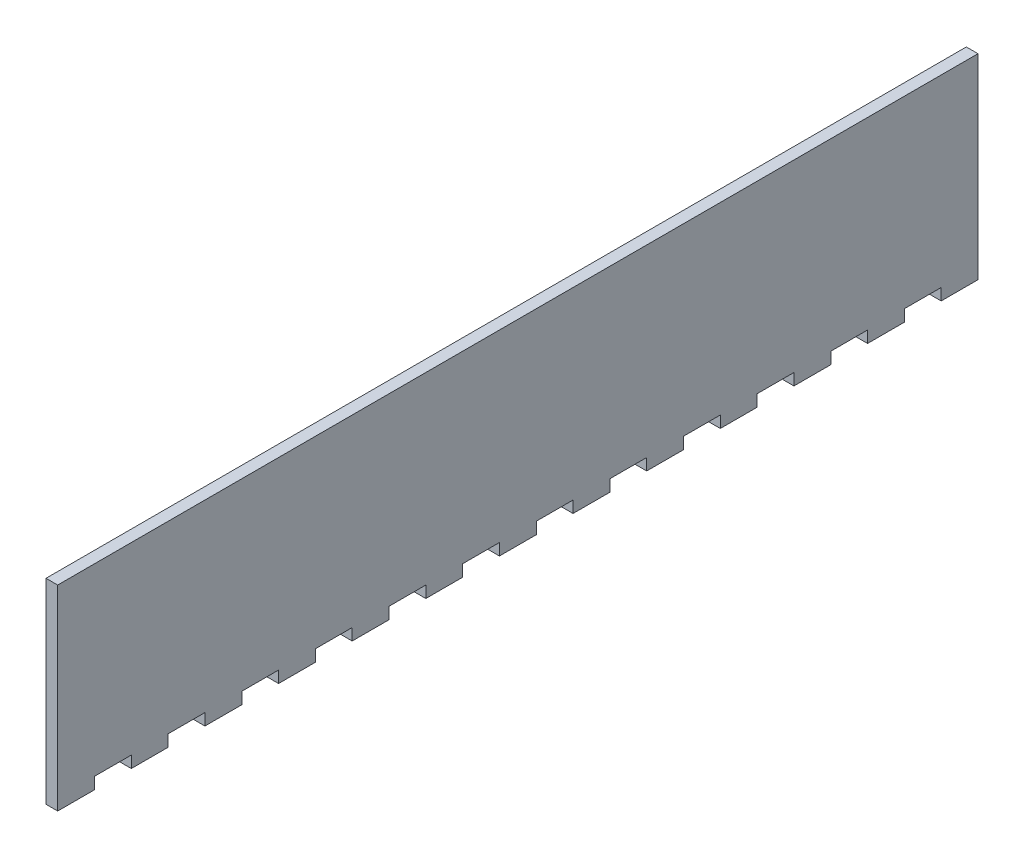
SolidWorks part; units mm, degrees
ref_plane "Plan de face" through (0, 0, 0) normal (0, 0, 1) x (1, 0, 0)
ref_plane "Plan de dessus" through (0, 0, 0) normal (0, 1, 0) x (1, 0, 0)
ref_plane "Plan de droite" through (0, 0, 0) normal (1, 0, 0) x (0, 0, -1)
sketch "Esquisse2" plane through (0, 0, 0) normal (1, 0, 0) x (0, 0, -1)
  line L1 (0, 0) -> (250, 0)
  line L2 (0, 0) -> (0, 50)
  line L3 (0, 50) -> (250, 50)
  line L4 (250, 0) -> (250, 50)
  dimension "D1" = 250
  dimension "D2" = 50
extrude "Boss.-Extru.1" add sketch "Esquisse2" along normal blind 3.175
sketch "Esquisse3" plane through (3.175, 0, 0) normal (1, 0, 0) x (0, 0, -1)
  line L1 (0, 0) -> (10, 0)
  line L2 (0, 0) -> (0, -3.175)
  line L3 (0, -3.175) -> (10, -3.175)
  line L4 (10, 0) -> (10, -3.175)
  dimension "D1" = 10
  dimension "D2" = 3.175
extrude "Boss.-Extru.2" add sketch "Esquisse3" against normal blind 3.175
pattern_linear "Répétition linéaire1" count 13 spacing 20 along (0, 0, -1) of "Boss.-Extru.2"
